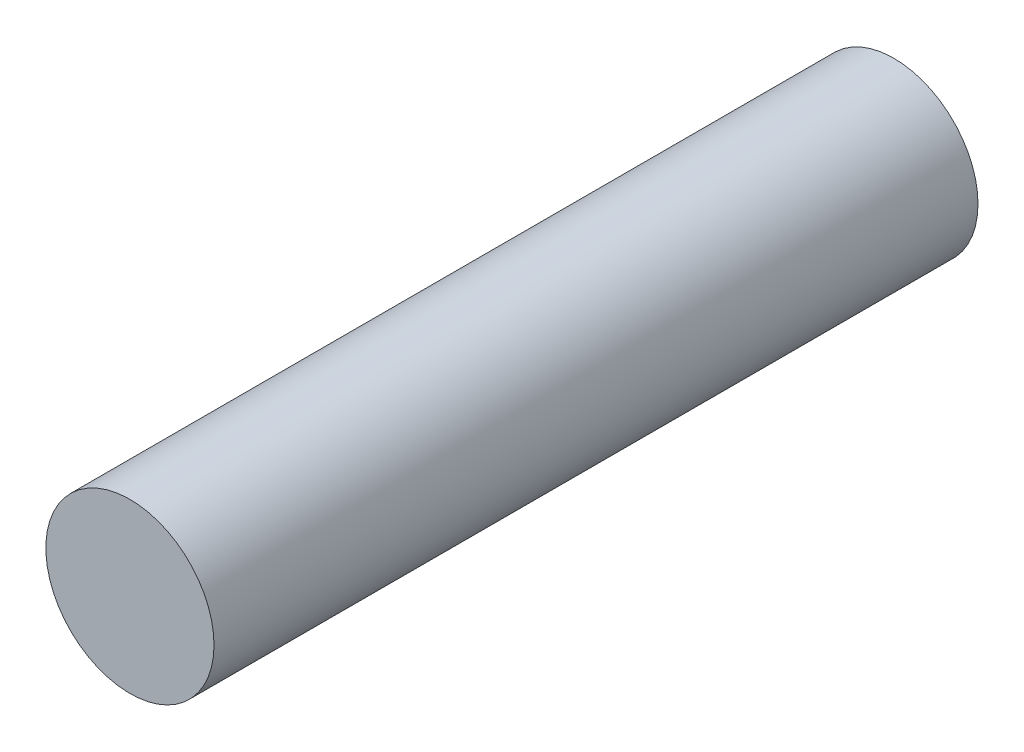
SolidWorks part; units mm, degrees
material "Beryllium"
ref_plane "Front Plane" through (0, 0, 0) normal (0, 0, 1) x (1, 0, 0)
ref_plane "Top Plane" through (0, 0, 0) normal (0, 1, 0) x (1, 0, 0)
ref_plane "Right Plane" through (0, 0, 0) normal (1, 0, 0) x (0, 0, -1)
sketch "Sketch1" plane through (0, 0, 0) normal (0, 0, 1) x (1, 0, 0)
  circle A0 centre (0, 0) radius 16.51
  dimension "D1" = 33.02
extrude "Boss-Extrude1" add sketch "Sketch1" along normal blind 150
